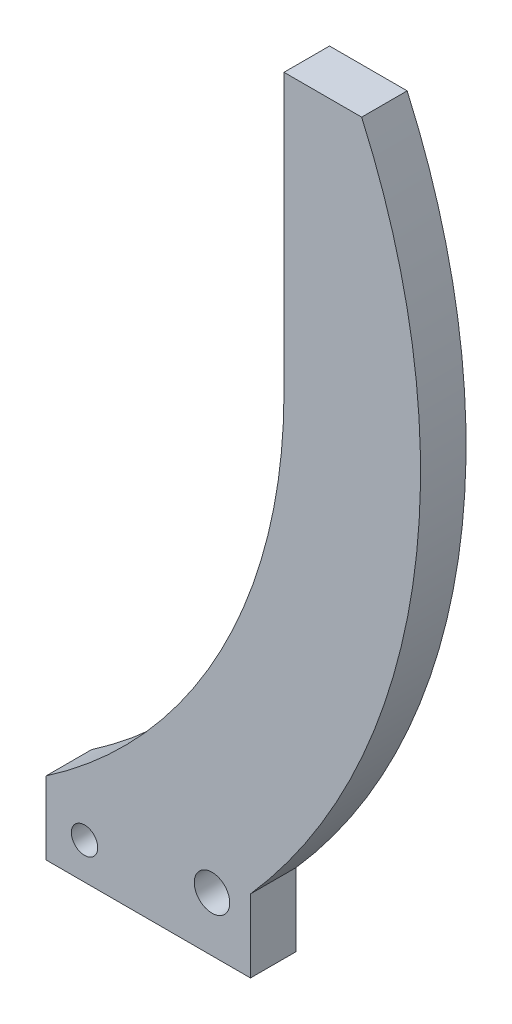
SolidWorks part; units mm, degrees
ref_plane "Front Plane" through (0, 0, 0) normal (0, 0, 1) x (1, 0, 0)
ref_plane "Top Plane" through (0, 0, 0) normal (0, 1, 0) x (1, 0, 0)
ref_plane "Right Plane" through (0, 0, 0) normal (1, 0, 0) x (0, 0, -1)
sketch "Sketch1" plane through (0, 0, 0) normal (0, 0, 1) x (1, 0, 0)
  line L0 (60, 30.4708) -> (68.5312, 30.4708)
  line L1 (33.8653, -49.5292) -> (56.3193, -49.5292) construction
  line L3 (56.3193, -49.5292) -> (56.3193, -57.5292)
  line L4 (33.8653, -49.5292) -> (33.8653, -57.5292)
  line L5 (56.3193, -57.5292) -> (33.8653, -57.5292)
  line L6 (33.8653, -53.5292) -> (56.3193, -53.5292) construction
  line L7 (60, 0) -> (60, 30.4708)
  line L8 (45.0923, -49.5292) -> (45.0923, -57.5292) construction
  circle A0 centre (0, 0) radius 60 construction
  arc A1 (56.3193, -49.5292) -> (68.5312, 30.4708) centre (0, 0) ccw
  arc A2 (33.8653, -49.5292) -> (60, 0) centre (0, 0) ccw
  circle A3 centre (38.0923, -53.5292) radius 1.45
  circle A4 centre (52.0923, -51.5292) radius 1.95
  point P7 (45.0923, -53.5292)
  dimension "D1" = 120
  dimension "D2" = 60
  dimension "D3" = 75
  dimension "D5" = 8
  dimension "D6" = 2.9
  dimension "D7" = 14
  dimension "D8" = 3.9
  dimension "D4" = 80
  dimension "D9" = 7
  dimension "D10" = 2
extrude "Boss-Extrude1" add sketch "Sketch1" along normal blind 5
